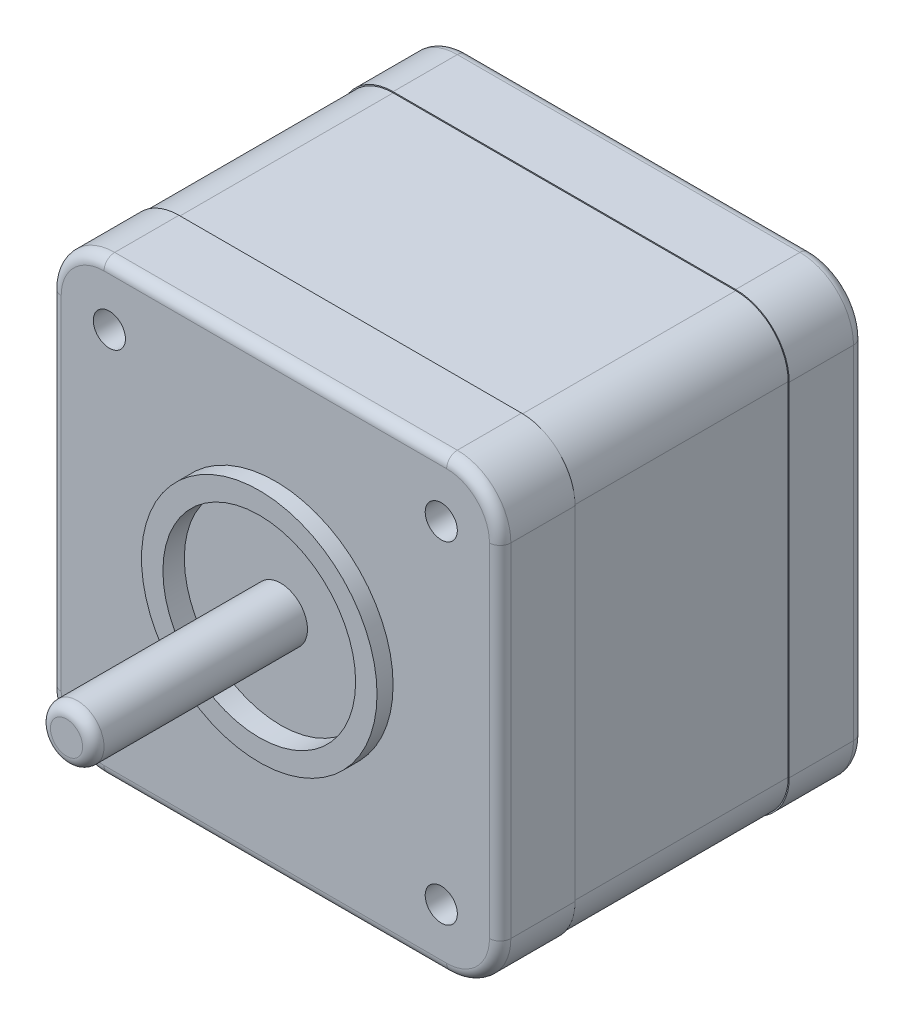
SolidWorks part; units mm, degrees
ref_plane "Front Plane" through (0, 0, 0) normal (0, 0, 1) x (1, 0, 0)
ref_plane "Top Plane" through (0, 0, 0) normal (0, 1, 0) x (1, 0, 0)
ref_plane "Right Plane" through (0, 0, 0) normal (1, 0, 0) x (0, 0, -1)
sketch "Sketch2" plane through (0, 0, 0) normal (0, 0, 1) x (1, 0, 0)
  line L1 (-16, -21) -> (16, -21)
  line L2 (-21, -16) -> (-21, 16)
  line L3 (-16, 21) -> (16, 21)
  line L4 (21, -16) -> (21, 16)
  line L5 (-21, -21) -> (21, 21) construction
  line L6 (-21, 21) -> (21, -21) construction
  arc A0 (16, 21) -> (21, 16) centre (16, 16) cw
  arc A1 (16, -21) -> (21, -16) centre (16, -16) ccw
  arc A2 (-16, -21) -> (-21, -16) centre (-16, -16) cw
  arc A3 (-21, 16) -> (-16, 21) centre (-16, 16) cw
  point P0 (0, 0)
  dimension "D2" = 5
  dimension "D1" = 42
extrude "Boss-Extrude1" add sketch "Sketch2" along normal blind 34
sketch "Sketch4" plane through (0, 0, 34) normal (0, 0, 1) x (1, 0, 0)
  circle A0 centre (0, 0) radius 11
  dimension "D1" = 22
extrude "Boss-Extrude2" add sketch "Sketch4" along normal blind 1.5
sketch "Sketch5" plane through (0, -21, 0) normal (0, -1, 0) x (1, 0, 0)
  line L1 (-7.5, 10) -> (7.5, 10)
  line L2 (-7.5, 10) -> (-7.5, 4)
  line L3 (-7.5, 4) -> (7.5, 4)
  line L4 (7.5, 10) -> (7.5, 4)
  line L5 (-7.5, 10) -> (7.5, 4) construction
  line L6 (-7.5, 4) -> (7.5, 10) construction
  line L7 (0, 7) -> (0, 0) construction
  line L8 (-16, 0) -> (16, 0) construction
  point P0 (0, 7)
  point P5 (0, 4.8954)
  point P10 (0, 3.0464)
  dimension "D1" = 15
  dimension "D2" = 6
  dimension "D3" = 4
extrude "Boss-Extrude3" add sketch "Sketch5" along normal blind 6
sketch "Sketch6" plane through (0, 0, 35.5) normal (0, 0, 1) x (1, 0, 0)
  circle A2 centre (0, 0) radius 9
  circle A3 centre (0, 0) radius 9
  dimension "D1" = 2
extrude "Cut-Extrude1" cut sketch "Sketch6" against normal blind 2
sketch "Sketch7" plane through (0, 0, 33.5) normal (0, 0, 1) x (1, 0, 0)
  circle A0 centre (0, 0) radius 2.5
  dimension "D1" = 5
extrude "Boss-Extrude4" add sketch "Sketch7" along normal blind 20
ref_plane "Plane1" through (0, 0, 27) normal (0, 0, 1) x (1, 0, 0)
sketch "Sketch8" plane through (0, 0, 27) normal (0, 0, 1) x (1, 0, 0)
  line L8 (16, 20.9) -> (-16, 20.9)
  line L9 (-20.9, 16) -> (-20.9, -16)
  line L10 (-16, -20.9) -> (16, -20.9)
  line L11 (20.9, -16) -> (20.9, 16)
  line L12 (16, 20.9) -> (-16, 20.9)
  line L13 (-20.9, 16) -> (-20.9, -16)
  line L14 (-16, -20.9) -> (16, -20.9)
  line L15 (20.9, -16) -> (20.9, 16)
  line L16 (16, 21) -> (-16, 21)
  line L17 (-21, 16) -> (-21, -16)
  line L18 (-16, -21) -> (16, -21)
  line L19 (21, -16) -> (21, 16)
  line L20 (16, 21) -> (-16, 21)
  line L21 (-21, 16) -> (-21, -16)
  line L22 (-16, -21) -> (16, -21)
  line L23 (21, -16) -> (21, 16)
  arc A8 (20.9, 16) -> (16, 20.9) centre (16, 16) ccw
  arc A9 (-16, 20.9) -> (-20.9, 16) centre (-16, 16) ccw
  arc A10 (-20.9, -16) -> (-16, -20.9) centre (-16, -16) ccw
  arc A11 (16, -20.9) -> (20.9, -16) centre (16, -16) ccw
  arc A12 (20.9, 16) -> (16, 20.9) centre (16, 16) ccw
  arc A13 (-16, 20.9) -> (-20.9, 16) centre (-16, 16) ccw
  arc A14 (-20.9, -16) -> (-16, -20.9) centre (-16, -16) ccw
  arc A15 (16, -20.9) -> (20.9, -16) centre (16, -16) ccw
  arc A16 (21, 16) -> (16, 21) centre (16, 16) ccw
  arc A17 (-16, 21) -> (-21, 16) centre (-16, 16) ccw
  arc A18 (-21, -16) -> (-16, -21) centre (-16, -16) ccw
  arc A19 (16, -21) -> (21, -16) centre (16, -16) ccw
  arc A20 (21, 16) -> (16, 21) centre (16, 16) ccw
  arc A21 (-16, 21) -> (-21, 16) centre (-16, 16) ccw
  arc A22 (-21, -16) -> (-16, -21) centre (-16, -16) ccw
  arc A23 (16, -21) -> (21, -16) centre (16, -16) ccw
  dimension "D1" = 0.1
  dimension "D2" = 0
extrude "Cut-Extrude3" cut sketch "Sketch8" against normal blind 20
fillet "Fillet1" radius 1 16 edges at (19.5355, 19.5355, 0) (21, 0, 0) (19.5355, -19.5355, 0) (0, -21, 0) (-19.5355, -19.5355, 0) (-21, 0, 0) (-19.5355, 19.5355, 0) (-19.5355, 19.5355, 34) (0, 21, 34) (19.5355, 19.5355, 34) (21, 0, 34) (19.5355, -19.5355, 34) (0, -21, 34) (-19.5355, -19.5355, 34) (0, 21, 0) (-21, 0, 34)
fillet "Fillet2" radius 1 1 edges at (2.5, 0, 53.5)
sketch "Sketch9" plane through (0, 0, 34) normal (0, 0, 1) x (1, 0, 0)
  line L1 (-15.5, 15.5) -> (15.5, 15.5) construction
  line L2 (-15.5, 15.5) -> (-15.5, -15.5) construction
  line L3 (-15.5, -15.5) -> (15.5, -15.5) construction
  line L4 (15.5, 15.5) -> (15.5, -15.5) construction
  line L5 (-15.5, 15.5) -> (15.5, -15.5) construction
  line L6 (-15.5, -15.5) -> (15.5, 15.5) construction
  circle A0 centre (15.5, 15.5) radius 1.5
  circle A1 centre (15.5, -15.5) radius 1.5
  circle A2 centre (-15.5, -15.5) radius 1.5
  circle A3 centre (-15.5, 15.5) radius 1.5
  point P0 (0, 0)
  dimension "D2" = 3
  dimension "D1" = 31
extrude "Cut-Extrude4" cut sketch "Sketch9" against normal blind 20
